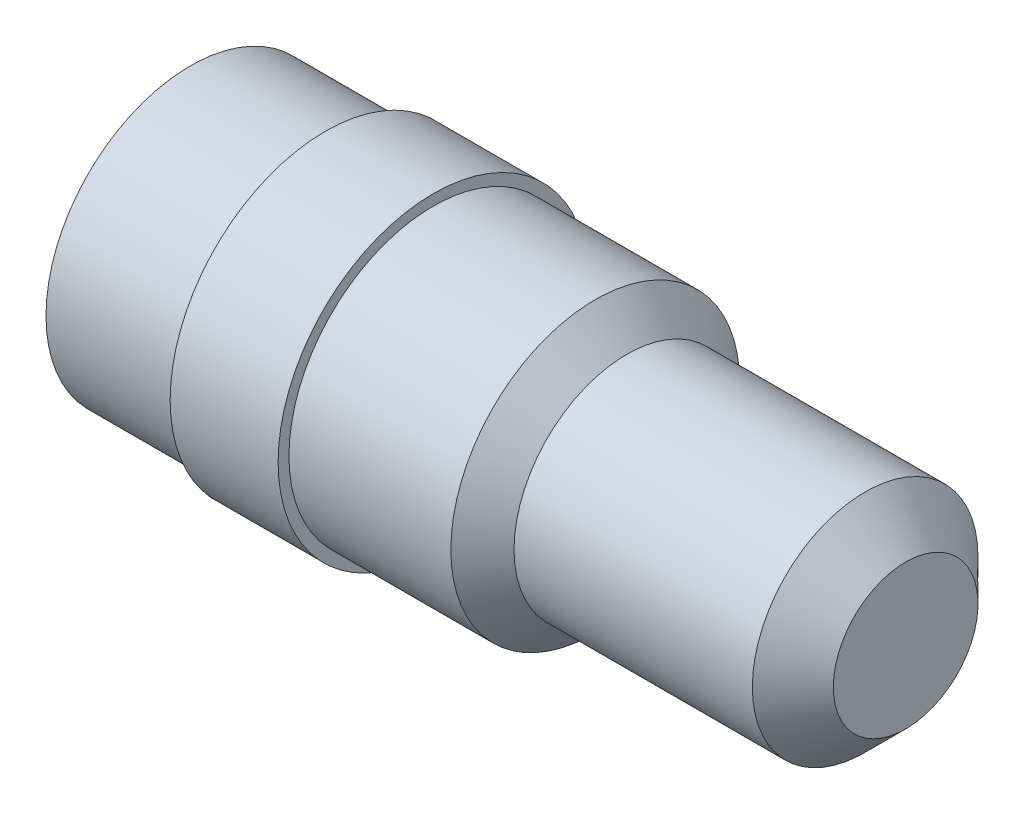
SolidWorks part; units mm, degrees
ref_plane "Front Plane" through (0, 0, 0) normal (0, 0, 1) x (1, 0, 0)
ref_plane "Top Plane" through (0, 0, 0) normal (0, 1, 0) x (1, 0, 0)
ref_plane "Right Plane" through (0, 0, 0) normal (1, 0, 0) x (0, 0, -1)
sketch "Sketch1" plane through (0, 0, 0) normal (0, 0, 1) x (1, 0, 0)
  line L0 (0, 0) -> (26.5, 0)
  line L1 (26.5, 0) -> (26.5, 2.68)
  line L2 (26.5, 2.68) -> (25, 4.18)
  line L3 (25, 4.18) -> (16.17, 4.18)
  line L4 (16.17, 4.18) -> (15, 5.35)
  line L5 (15, 5.35) -> (9, 5.35)
  line L6 (9, 5.35) -> (9, 5.75)
  line L7 (9, 5.75) -> (5, 5.75)
  line L8 (5, 5.75) -> (5, 5.35)
  line L9 (5, 5.35) -> (0, 5.35)
  line L10 (0, 5.35) -> (0, 0)
  point P2 (7.8176, 3.0683)
  point P13 (0, 0)
  point P14 (6, 4.6247)
  point P15 (-9, 0.4447)
  point P16 (17.5, 0.3113)
  point P17 (0, 0)
  point P18 (0, 0)
  point P19 (0, 0)
  point P20 (0, 0)
  dimension "D1" = 4.18
  dimension "D2" = 1.5
  dimension "D3" = 5.35
  dimension "D4" = 5.75
  dimension "D5" = 4
  dimension "D6" = 5
  dimension "D7" = 15
  dimension "D8" = 45
  dimension "D9" = 26.5
revolve "Revolve1" add sketch "Sketch1" angle 360 about L0
